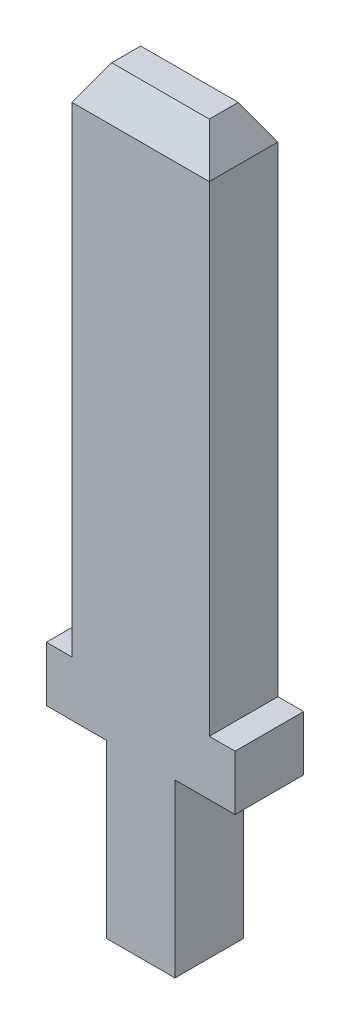
SolidWorks part; units mm, degrees
material "Медь"
ref_plane "Спереди" through (0, 0, 0) normal (0, 0, 1) x (1, 0, 0)
ref_plane "Сверху" through (0, 0, 0) normal (0, 1, 0) x (1, 0, 0)
ref_plane "Справа" through (0, 0, 0) normal (1, 0, 0) x (0, 0, -1)
sketch "Эскиз1" plane through (0, 0, 0) normal (0, 0, 1) x (1, 0, 0)
  line L0 (1, 0) -> (-1, 0)
  line L1 (-1, 0) -> (-1, 5)
  line L2 (-1, 5) -> (-2.75, 5)
  line L3 (-2.75, 5) -> (-2.75, 6.6)
  line L4 (-2.75, 6.6) -> (-2, 6.6)
  line L5 (-2, 6.6) -> (-2, 21.6)
  line L6 (-2, 21.6) -> (2, 21.6)
  line L7 (0, 21.6) -> (0, 0) construction
  line L8 (2, 6.6) -> (2, 21.6)
  line L9 (2.75, 6.6) -> (2, 6.6)
  line L10 (2.75, 5) -> (2.75, 6.6)
  line L11 (1, 5) -> (2.75, 5)
  line L12 (1, 0) -> (1, 5)
  dimension "D1" = 15
  dimension "D2" = 2
  dimension "D3" = 2.75
  dimension "D4" = 1.6
  dimension "D5" = 5
  dimension "D6" = 1
extrude "Бобышка-Вытянуть1" add sketch "Эскиз1" along normal mid plane 2
chamfer "Фаска1" distance 1 angle 30 4 edges at (2, 21.6, 0) (0, 21.6, 1) (-2, 21.6, 0) (0, 21.6, -1)
